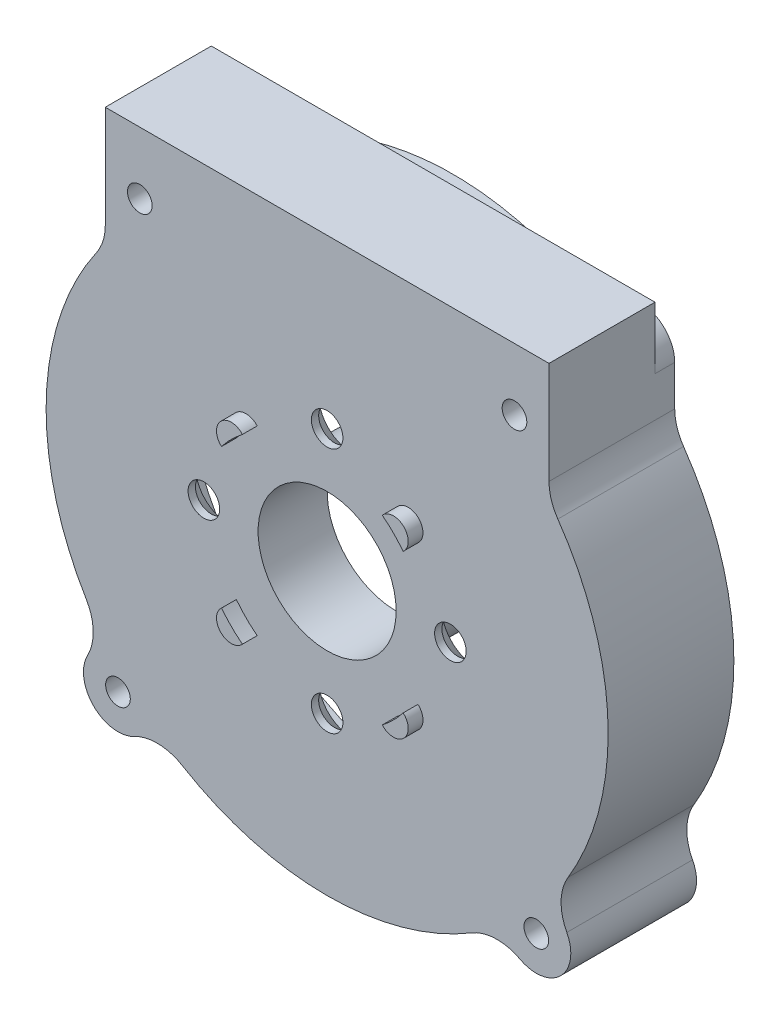
SolidWorks part; units mm, degrees
material "6061 Alloy"
ref_plane "Front" through (0, 0, 0) normal (0, 0, 1) x (1, 0, 0)
ref_plane "Top" through (0, 0, 0) normal (0, 1, 0) x (1, 0, 0)
ref_plane "Right" through (0, 0, 0) normal (1, 0, 0) x (0, 0, -1)
sketch "Sketch1" plane through (0, 0, 0) normal (1, 0, 0) x (0, 0, -1)
  line L0 (0, 0) -> (31.3333, 0) construction
  line L1 (5.9299, 28.5) -> (-0.4583, 28.5)
  line L2 (-0.4583, 28.5) -> (-0.4583, 17.5)
  line L4 (-0.4583, 17.5) -> (-0.4583, 7)
  line L5 (-0.4583, 7) -> (6.5417, 7)
  line L6 (6.5417, 7) -> (6.5417, 8.5)
  line L7 (6.5417, 8.5) -> (2.5417, 8.5)
  line L8 (2.5417, 8.5) -> (2.5417, 9)
  line L9 (2.5417, 9) -> (2.0417, 9)
  line L10 (2.0417, 9) -> (2.0417, 15)
  line L12 (2.0417, 15) -> (2.0417, 26.5)
  line L13 (2.0417, 26.5) -> (6.7917, 26.5)
  line L14 (6.7917, 26.5) -> (6.7917, 27.5)
  line L15 (6.7917, 27.5) -> (12.2917, 27.5)
  line L16 (12.2917, 27.5) -> (12.2917, 28.5)
  line L17 (12.2917, 28.5) -> (5.9299, 28.5)
  dimension "D1" = 7
  dimension "D2" = 7
  dimension "D3" = 4
  dimension "D4" = 0.5
  dimension "D5" = 0.5
  dimension "D6" = 8.5
  dimension "D7" = 27.5
  dimension "D8" = 4.75
  dimension "D9" = 2.5
  dimension "D10" = 5.5
  dimension "D12" = 2
  dimension "D14" = 1
revolve "Revolve1" add sketch "Sketch1" angle 360 about L0
sketch "Sketch2" plane through (0, 0, -2.0417) normal (0, 0, -1) x (-1, 0, 0)
  circle A0 centre (0, 0) radius 9 construction
  point P0 (0, 12.5)
  point P3 (12.5, 0)
  point P6 (0, -12.5)
  point P7 (-12.5, 0)
  point P8 (0, 0)
  dimension "D1" = 12.5
  dimension "D2" = 4
hole_wizard "CSK for M3 SFHCS1" positions "3DSketch1" profile "Sketch3" countersink size "M3" standard "ANSI Metric" end condition through all
sketch3d "3DSketch1"
  point P0 (0, 12.5, -2.0417)
  point P3 (-12.5, 0, -2.0417)
  point P6 (0, -12.5, -2.0417)
  point P9 (12.5, 0, -2.0417)
sketch "Sketch3" plane through (0, 12.5, -2.0417) normal (1, 0, 0) x (0, 1, 0)
  line L0 (0, 0) -> (0, 2.5)
  line L1 (0, 2.5) -> (1.6, 2.5)
  line L2 (1.6, 2.5) -> (1.6, 1.76)
  line L3 (1.6, 1.76) -> (3.36, 0)
  line L5 (3.36, 0) -> (0, 0)
  line L6 (-1.6, 1.76) -> (-3.36, 0) construction
  line L11 (0, -6.35) -> (0, 107.95) construction
  dimension "Thru Hole Dia." = 3.2
  dimension "Thru Hole Depth" = 2.5
  dimension "Near C'Sink Dia." = 6.72
  dimension "Near C'Sink Angle" = 90
sketch "Sketch11" plane through (0, 0, 0.4583) normal (0, 0, 1) x (1, 0, 0)
  line L1 (-22.5, 16.2973) -> (22.5, 16.2973)
  line L2 (-22.5, 16.2973) -> (-22.5, 29.5)
  line L3 (-22.5, 29.5) -> (22.5, 29.5)
  line L4 (22.5, 16.2973) -> (22.5, 29.5)
  line L5 (-22.5, 16.2973) -> (22.5, 29.5) construction
  line L6 (-22.5, 29.5) -> (22.5, 16.2973) construction
  circle A0 centre (0, 0) radius 28.5 construction
  point P0 (0, 22.8986)
  point P5 (0, 28.5)
  circle M8 centre (0, 0) radius 28.5
  dimension "D1" = 1
  dimension "D2" = 45
extrude "Boss-Extrude3" add sketch "Sketch11" against normal offset from surface (10.75 mm away) 2 contours L4 L3 L2 M8 up to face at (28.5, 0, -12.2917)
sketch "Sketch12" plane through (0, 0, -10.2917) normal (0, 0, -1) x (-1, 0, 0)
  line L0 (-22.5, 29.5) -> (-22.5, 17.4929) construction
  line L1 (22.5, 29.5) -> (22.5, 17.4929) construction
  line L2 (-22.5, 23.2164) -> (-22.5, 15.2649)
  line L3 (-22.5, 15.2649) -> (22.5, 15.2649)
  line L4 (22.5, 15.2649) -> (22.5, 23.2164)
  line L5 (-19, 26.7164) -> (19, 26.7164)
  circle A0 centre (-19, 23.2164) radius 1.5
  circle A1 centre (-19, 23.2164) radius 3.5
  circle A2 centre (19, 23.2164) radius 1.5
  circle A3 centre (19, 23.2164) radius 3.5
  arc A4 (22.5, 17.4929) -> (-22.5, 17.4929) centre (0, 0) ccw construction
  circle A5 centre (0, 0) radius 27.7592
  line M1 (22.5, 17.4929) -> (22.5, 29.5)
  line M3 (-22.5, 29.5) -> (-22.5, 17.4929)
  arc M5 (-22.5, 17.4929) -> (22.5, 17.4929) centre (0, 0) cw
  dimension "D1" = 7
  dimension "D2" = 7
  dimension "D3" = 3
  dimension "D4" = 3
extrude "Boss-Extrude7" add sketch "Sketch12" along normal up to surface (2 mm away) contours A5 A1 M5 | A1 A0 M5 | A1 M3 M5 | A5 A3 M5 | A3 A2 M5 | A3 M5 M1 up to face at (28.5, 0, -12.2917)
fillet "Fillet6" radius 5 4 edges at (-22.5, 17.4929, -5.9167) (22.5, 17.4929, -5.9167) (-15.5627, 23.8758, -11.2917) (15.5627, 23.8758, -11.2917)
sketch "Sketch14" plane through (0, 0, -12.2917) normal (0, 0, -1) x (-1, 0, 0)
  circle A0 centre (-19, 23.2164) radius 1.25
  circle A1 centre (19, 23.2164) radius 1.25
  dimension "D1" = 2.5
  dimension "D2" = 2.5
extrude "Cut-Extrude2" cut sketch "Sketch14" against normal through all
sketch "Sketch15" plane through (0, 0, 0.4583) normal (0, 0, 1) x (1, 0, 0)
  line L0 (0, 0) -> (21.2132, -21.2132) construction
  line L1 (0, 0) -> (7, 0) construction
  line L2 (-21.2132, -21.2132) -> (0, 0) construction
  circle A0 centre (21.2132, -21.2132) radius 3.5
  circle A1 centre (0, 0) radius 7 construction
  circle A2 centre (-21.2132, -21.2132) radius 3.5
  arc A3 (-23.3955, 16.2757) -> (23.3955, 16.2757) centre (0, 0) ccw construction
  point P9 (-20.1525, -20.1525)
  point P10 (20.1525, -20.1525)
  arc M17 (-23.3955, 16.2757) -> (23.3955, 16.2757) centre (0, 0) ccw
  dimension "D1" = 7
  dimension "D3" = 7
  dimension "D2" = 45
  dimension "D4" = 90
  dimension "D5" = 1.5
extrude "Boss-Extrude8" add sketch "Sketch15" against normal up to surface (12.75 mm away) contours A0 M17 | A2 M17
sketch "Sketch16" plane through (0, 0, -12.2917) normal (0, 0, -1) x (-1, 0, 0)
  circle A0 centre (-21.2132, -21.2132) radius 1.25
  circle A1 centre (21.2132, -21.2132) radius 1.25
  dimension "D1" = 2.5
  dimension "D2" = 2.5
extrude "Cut-Extrude3" cut sketch "Sketch16" against normal through all
fillet "Fillet8" radius 5 4 edges at (22.211, -17.8584, -5.9167) (17.8584, -22.211, -5.9167) (-17.8584, -22.211, -5.9167) (-22.211, -17.8584, -5.9167)
sketch "Sketch17" plane through (0, 0, 0.4583) normal (0, 0, 1) x (1, 0, 0)
  line L0 (0, 0) -> (8.2201, 8.2201) construction
  line L1 (0, 0) -> (12.5, 0) construction
  circle A0 centre (8.2201, 8.2201) radius 1.5
  circle A1 centre (8.2201, -8.2201) radius 1.5
  circle A2 centre (-8.2201, -8.2201) radius 1.5
  circle A3 centre (-8.2201, 8.2201) radius 1.5
  point P3 (7.1595, 7.1595)
  point P16 (0, 0)
  dimension "D3" = 3
  dimension "D1" = 45
  dimension "D2" = 11.625
  dimension "D4" = 4
extrude "Boss-Extrude9" add sketch "Sketch17" along normal blind 1.5
sketch "Sketch18" plane through (0, 0, 1.9583) normal (0, 0, 1) x (1, 0, 0)
  point P0 (0, 0)
sketch "Sketch19" plane through (0, 0, -12.2917) normal (0, 0, -1) x (-1, 0, 0)
  point P0 (0, 0)
sketch "Sketch20" plane through (0, 0, 1.9583) normal (0, 0, 1) x (1, 0, 0)
  circle A0 centre (0, 0) radius 11.625
extrude "Cut-Extrude4" cut sketch "Sketch20" against normal up to surface (1.5 mm away) up to face at (-9.7201, 8.2201, 0.4583)
